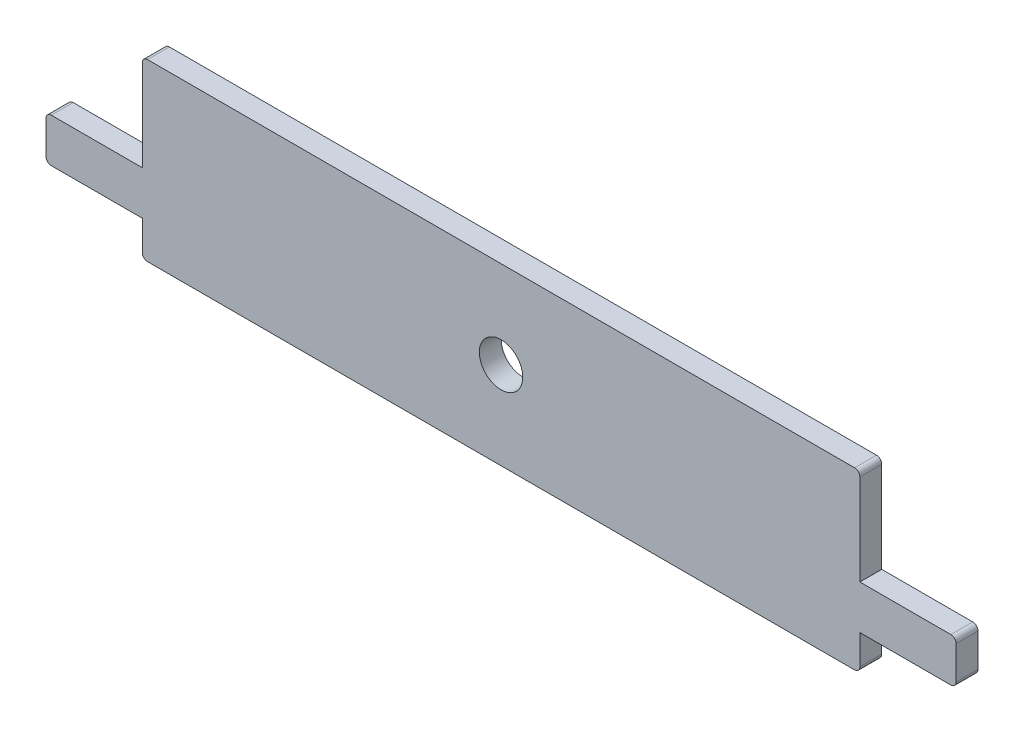
SolidWorks part; units mm, degrees
ref_plane "Front Plane" through (0, 0, 0) normal (0, 0, 1) x (1, 0, 0)
ref_plane "Top Plane" through (0, 0, 0) normal (0, 1, 0) x (1, 0, 0)
ref_plane "Right Plane" through (0, 0, 0) normal (1, 0, 0) x (0, 0, -1)
sketch "Sketch1" plane through (0, 0, 0) normal (0, 0, 1) x (1, 0, 0)
  line L0 (52.07, 25.4) -> (52.07, 0) construction
  line L1 (0.762, 0) -> (103.378, 0)
  line L2 (0, 0.762) -> (0, 5.08)
  line L3 (0.762, 25.4) -> (103.378, 25.4)
  line L4 (104.14, 0.762) -> (104.14, 5.08)
  line L5 (-13.208, 5.08) -> (0, 5.08)
  line L6 (-13.97, 5.842) -> (-13.97, 10.668)
  line L7 (-13.208, 11.43) -> (0, 11.43)
  line L8 (118.11, 5.842) -> (118.11, 10.668)
  line L9 (-13.97, 8.255) -> (118.11, 8.255) construction
  line L10 (0, 11.43) -> (0, 24.638)
  line L11 (104.14, 11.43) -> (117.348, 11.43)
  line L12 (104.14, 11.43) -> (104.14, 24.638)
  line L13 (104.14, 5.08) -> (117.348, 5.08)
  arc A0 (103.378, 0) -> (104.14, 0.762) centre (103.378, 0.762) ccw
  arc A1 (0.762, 0) -> (0, 0.762) centre (0.762, 0.762) cw
  arc A2 (-13.208, 5.08) -> (-13.97, 5.842) centre (-13.208, 5.842) cw
  arc A3 (-13.97, 10.668) -> (-13.208, 11.43) centre (-13.208, 10.668) cw
  arc A4 (117.348, 5.08) -> (118.11, 5.842) centre (117.348, 5.842) ccw
  arc A5 (117.348, 11.43) -> (118.11, 10.668) centre (117.348, 10.668) cw
  arc A6 (103.378, 25.4) -> (104.14, 24.638) centre (103.378, 24.638) cw
  arc A7 (0, 24.638) -> (0.762, 25.4) centre (0.762, 24.638) cw
  circle A8 centre (52.07, 12.7) radius 3.1496
  point P21 (0, 0)
  point P24 (-13.97, 5.08)
  point P27 (-13.97, 11.43)
  point P34 (104.14, 25.4)
  point P37 (0, 25.4)
  dimension "D6" = 0.762
  dimension "D7" = 6.2992
  dimension "D1" = 25.4
  dimension "D2" = 104.14
  dimension "D3" = 6.35
  dimension "D4" = 132.08
  dimension "D5" = 17.145
extrude "Boss-Extrude1" add sketch "Sketch1" along normal blind 3.175
